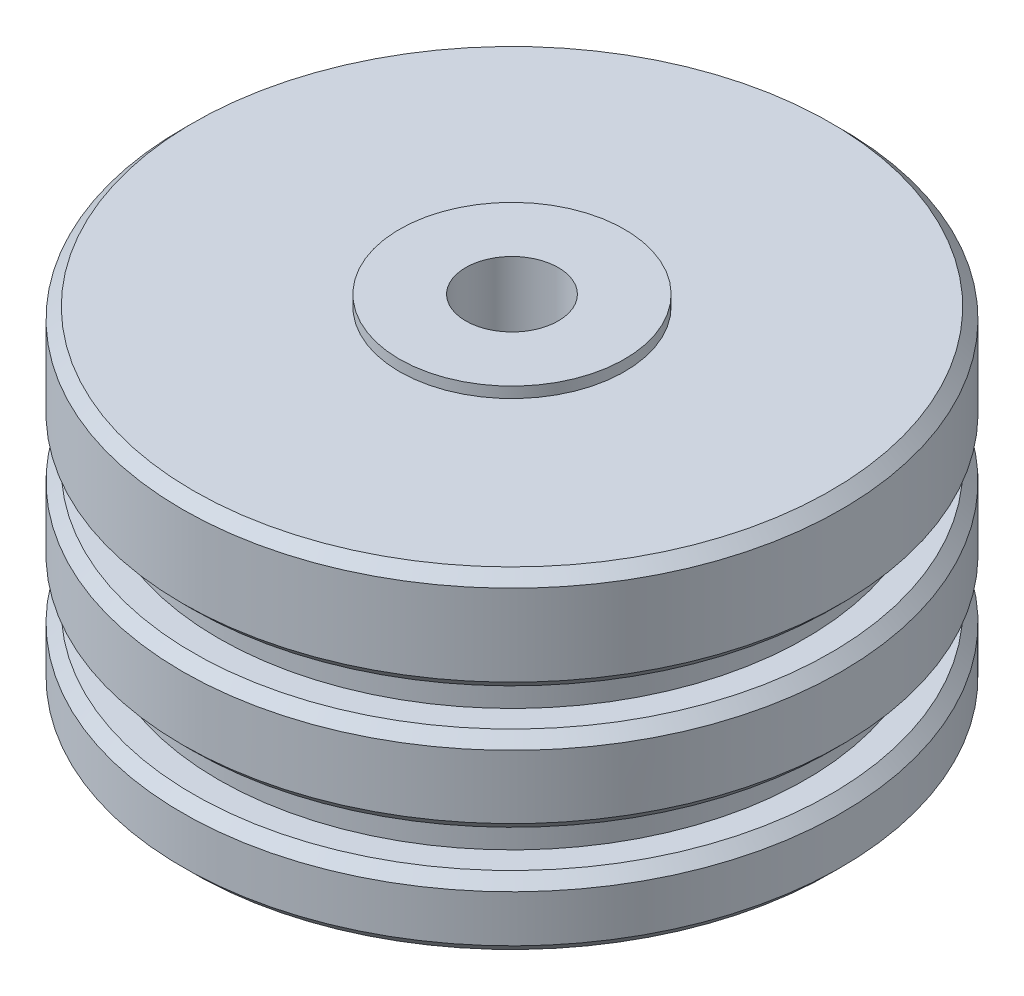
SolidWorks part; units mm, degrees
ref_plane "Front Plane" through (0, 0, 0) normal (0, 0, 1) x (1, 0, 0)
ref_plane "Top Plane" through (0, 0, 0) normal (0, 1, 0) x (1, 0, 0)
ref_plane "Right Plane" through (0, 0, 0) normal (1, 0, 0) x (0, 0, -1)
sketch "Sketch1" plane through (0, 0, 0) normal (0, 0, 1) x (1, 0, 0)
  line L0 (0, 0) -> (7.9375, 0)
  line L1 (23.241, 0.762) -> (23.241, 5.588)
  line L2 (23.241, 5.588) -> (20.701, 5.588)
  line L3 (20.701, 5.588) -> (20.701, 8.2268)
  line L4 (20.701, 8.2268) -> (23.241, 8.2268)
  line L5 (23.241, 8.2268) -> (23.241, 14.2268)
  line L6 (23.241, 14.2268) -> (20.701, 14.2268)
  line L7 (20.701, 14.2268) -> (20.701, 16.8656)
  line L8 (20.701, 16.8656) -> (23.241, 16.8656)
  line L9 (23.241, 16.8656) -> (23.241, 24.13)
  line L10 (7.9375, 24.892) -> (0, 24.892)
  line L11 (0, 24.892) -> (0, 0)
  line L12 (7.9375, 24.892) -> (7.9375, 24.13)
  line L13 (7.9375, 24.13) -> (23.241, 24.13)
  line L14 (23.241, 24.13) -> (23.241, 0.762)
  line L15 (23.241, 0.762) -> (7.9375, 0.762)
  line L16 (7.9375, 0.762) -> (7.9375, 0)
  point P15 (23.241, 11.2268)
  dimension "D1" = 6
  dimension "D3" = 24.892
  dimension "D4" = 23.241
  dimension "D5" = 2.54
  dimension "D2" = 11.2268
  dimension "D6" = 5.588
  dimension "D7" = 0.762
  dimension "D8" = 7.9375
revolve "Revolve1" add sketch "Sketch1" angle 360 about L11
hole_wizard "1/4 Clearance Hole1" positions "Sketch2" profile "Sketch3" hole size "1/4" standard "ANSI Inch" end condition through all
sketch "Sketch2" plane through (0, 24.892, 0) normal (0, 1, 0) x (1, 0, 0)
  point P0 (0, 0)
sketch "Sketch3" plane through (0, 24.892, 0) normal (1, 0, 0) x (0, 0, 1)
  line L0 (0, 0) -> (0, 24.892)
  line L1 (0, 24.892) -> (3.2639, 24.892)
  line L2 (3.2639, 24.892) -> (3.2639, 0)
  line L5 (3.2639, 0) -> (0, 0)
  line L11 (0, -6.35) -> (0, 107.95) construction
  dimension "Thru Hole Dia." = 6.5278
  dimension "Thru Hole Depth" = 24.892
chamfer "Chamfer1" distance 0.762 angle 45 6 edges at (0, 24.13, 23.241) (0, 16.8656, 23.241) (0, 14.2268, 23.241) (0, 8.2268, 23.241) (0, 5.588, 23.241) (0, 0.762, 23.241)
equation "\"D1@Sketch1\"=6mm"
